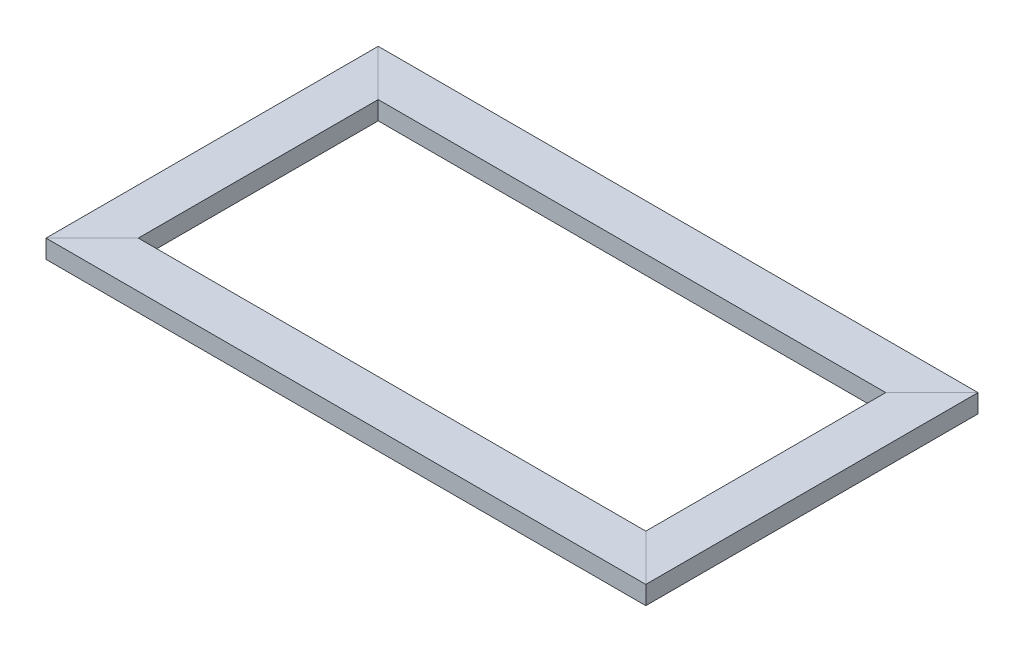
SolidWorks part; units mm, degrees
ref_plane "Front Plane" through (0, 0, 0) normal (0, 0, 1) x (1, 0, 0)
ref_plane "Top Plane" through (0, 0, 0) normal (0, 1, 0) x (1, 0, 0)
ref_plane "Right Plane" through (0, 0, 0) normal (1, 0, 0) x (0, 0, -1)
sketch "Sketch1" plane through (0, 0, 0) normal (1, 0, 0) x (0, 0, -1)
  line L1 (0, 0) -> (50, 0)
  line L2 (0, 0) -> (0, 20)
  line L3 (0, 20) -> (50, 20)
  line L4 (50, 0) -> (50, 20)
  dimension "D1" = 20
  dimension "D2" = 50
sketch3d "3DSketch1"
  line L0 (0, 0, 0) -> (650, 0, 0)
  line L1 (650, 0, 0) -> (650, 0, -360)
  line L2 (650, 0, -360) -> (0, 0, -360)
  line L3 (0, 0, -360) -> (0, 0, 0)
  dimension "D1" = 360
  dimension "D2" = 650
sweep "Sweep1" add profiles "Sketch1" path "3DSketch1"
